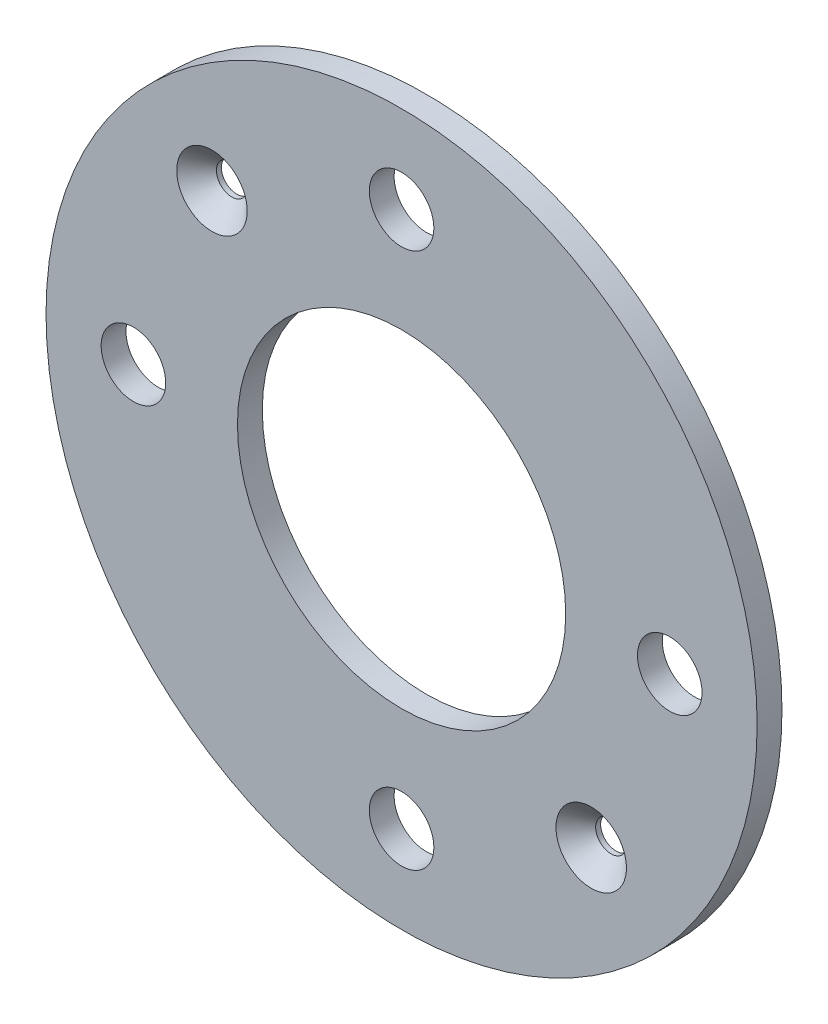
SolidWorks part; units mm, degrees
ref_plane "Plan de face" through (0, 0, 0) normal (0, 0, 1) x (1, 0, 0)
ref_plane "Plan de dessus" through (0, 0, 0) normal (0, 1, 0) x (1, 0, 0)
ref_plane "Plan de droite" through (0, 0, 0) normal (1, 0, 0) x (0, 0, -1)
sketch "Esquisse1" plane through (0, 0, 0) normal (0, 0, 1) x (1, 0, 0)
  circle A0 centre (0, 0) radius 71.6
  circle A1 centre (0, 0) radius 33.05
  dimension "D1" = 143.2
  dimension "D2" = 66.1
extrude "Boss.-Extru.1" add sketch "Esquisse1" along normal blind 5
sketch "Esquisse2" plane through (0, 0, 5) normal (0, 0, 1) x (1, 0, 0)
  circle A0 centre (0, 0) radius 54 construction
  circle A1 centre (0, 54) radius 6.5
  circle A2 centre (54, 0) radius 6.5
  circle A3 centre (-54, 0) radius 6.5
  circle A4 centre (0, -54) radius 6.5
  dimension "D1" = 108
  dimension "D2" = 13
extrude "Enlèv. mat.-Extru.1" cut sketch "Esquisse2" against normal through all
sketch "Esquisse3" plane through (0, 0, 5) normal (0, 0, 1) x (1, 0, 0)
  line L0 (-38.1838, 38.1838) -> (38.1838, -38.1838) construction
  line L1 (0, 0) -> (0, 54) construction
  circle A0 centre (0, 0) radius 54 construction
  circle A1 centre (-38.1838, 38.1838) radius 3.1
  circle A2 centre (38.1838, -38.1838) radius 3.1
  dimension "D1" = 45
  dimension "D2" = 6.2
extrude "Enlèv. mat.-Extru.2" cut sketch "Esquisse3" against normal through all
chamfer "Chanfrein1" distance 4 angle 45 2 edges at (41.2838, -38.1838, 5) (-35.0838, 38.1838, 5)
